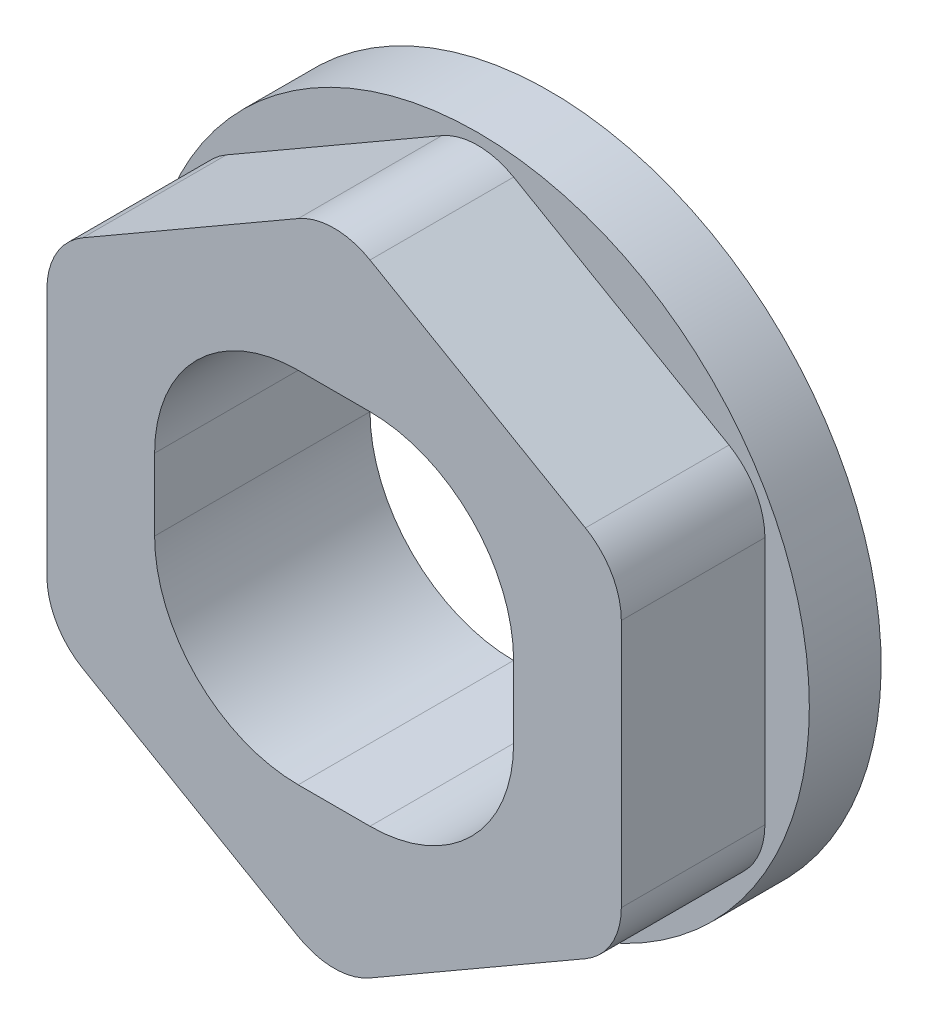
SolidWorks part; units mm, degrees
material "7075-T6 (SN)"
ref_plane "Front Plane" through (0, 0, 0) normal (0, 0, 1) x (1, 0, 0)
ref_plane "Top Plane" through (0, 0, 0) normal (0, 1, 0) x (1, 0, 0)
ref_plane "Right Plane" through (0, 0, 0) normal (1, 0, 0) x (0, 0, -1)
sketch "Sketch1" plane through (0, 0, 0) normal (0, 0, 1) x (1, 0, 0)
  line L1 (2.5, 12.5) -> (-2.5, 12.5)
  line L2 (12.5, 2.5) -> (12.5, -2.5)
  line L3 (2.5, -12.5) -> (-2.5, -12.5)
  line L4 (-12.5, 2.5) -> (-12.5, -2.5)
  line L5 (12.5, 12.5) -> (-12.5, -12.5) construction
  line L6 (12.5, -12.5) -> (-12.5, 12.5) construction
  line L7 (0, 23.094) -> (-20, 11.547)
  line L8 (-20, 11.547) -> (-20, -11.547)
  line L9 (-20, -11.547) -> (0, -23.094)
  line L10 (0, -23.094) -> (20, -11.547)
  line L11 (20, -11.547) -> (20, 11.547)
  line L12 (20, 11.547) -> (0, 23.094)
  arc A2 (12.5, -2.5) -> (2.5, -12.5) centre (2.5, -2.5) cw
  arc A3 (2.5, 12.5) -> (12.5, 2.5) centre (2.5, 2.5) cw
  arc A4 (-2.5, 12.5) -> (-12.5, 2.5) centre (-2.5, 2.5) ccw
  arc A5 (-2.5, -12.5) -> (-12.5, -2.5) centre (-2.5, -2.5) cw
  circle A6 centre (0, 0) radius 20 construction
  circle A7 centre (0, 0) radius 23.094
  dimension "D1" = 25
  dimension "D2" = 40
  dimension "D3" = 10
extrude "Boss-Extrude1" add sketch "Sketch1" along normal blind 10 contours L11 L12 L7 L8 L9 L10 L3 A5 L4 A4 L1 A3 L2 A2
sketch "Sketch2" plane through (0, 0, 0) normal (0, 0, -1) x (-1, 0, 0)
  line L0 (-2.5, 12.5) -> (2.5, 12.5) construction
  line L1 (12.5, 2.5) -> (12.5, -2.5) construction
  line L2 (-2.5, -12.5) -> (2.5, -12.5) construction
  line L3 (-12.5, 2.5) -> (-12.5, -2.5) construction
  line L4 (-2.5, 12.5) -> (2.5, 12.5)
  line L5 (12.5, 2.5) -> (12.5, -2.5)
  line L6 (-2.5, -12.5) -> (2.5, -12.5)
  line L7 (-12.5, 2.5) -> (-12.5, -2.5)
  circle A0 centre (0, 0) radius 23.094
  arc A1 (12.5, 2.5) -> (2.5, 12.5) centre (2.5, 2.5) ccw construction
  arc A2 (2.5, -12.5) -> (12.5, -2.5) centre (2.5, -2.5) ccw construction
  arc A3 (-12.5, -2.5) -> (-2.5, -12.5) centre (-2.5, -2.5) ccw construction
  arc A4 (-2.5, 12.5) -> (-12.5, 2.5) centre (-2.5, 2.5) ccw construction
  arc A5 (12.5, 2.5) -> (2.5, 12.5) centre (2.5, 2.5) ccw
  arc A6 (2.5, -12.5) -> (12.5, -2.5) centre (2.5, -2.5) ccw
  arc A7 (-12.5, -2.5) -> (-2.5, -12.5) centre (-2.5, -2.5) ccw
  arc A8 (-2.5, 12.5) -> (-12.5, 2.5) centre (-2.5, 2.5) ccw
extrude "Boss-Extrude2" add sketch "Sketch2" along normal blind 5
fillet "Fillet1" radius 5 6 edges at (-20, 11.547, 5) (-20, -11.547, 5) (0, -23.094, 5) (20, -11.547, 5) (20, 11.547, 5) (0, 23.094, 5)
